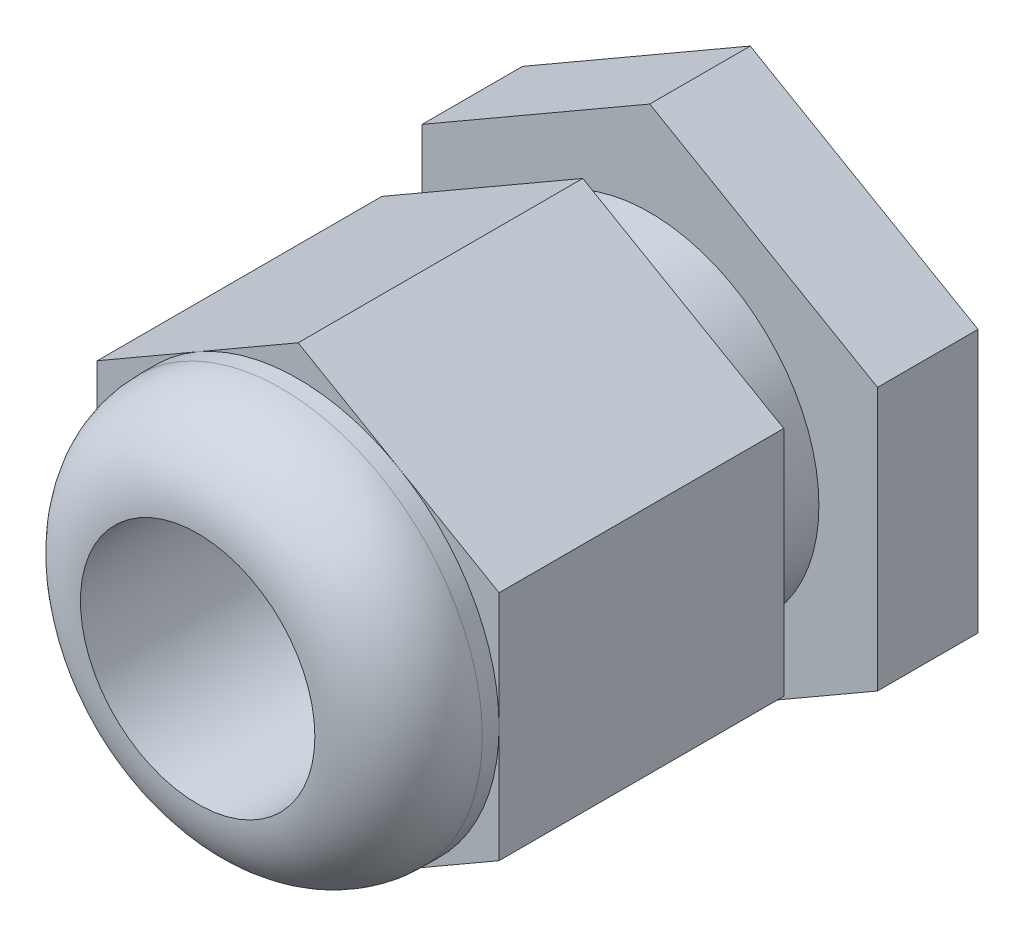
SolidWorks part; units mm, degrees
ref_plane "Plano frontal" through (0, 0, 0) normal (0, 0, 1) x (1, 0, 0)
ref_plane "Plano superior" through (0, 0, 0) normal (0, 1, 0) x (1, 0, 0)
ref_plane "Plano direito" through (0, 0, 0) normal (1, 0, 0) x (0, 0, -1)
sketch "Esboço1" plane through (0, 0, 0) normal (0, 0, 1) x (1, 0, 0)
  line L1 (0, 13.8564) -> (-12, 6.9282)
  line L2 (-12, 6.9282) -> (-12, -6.9282)
  line L3 (-12, -6.9282) -> (0, -13.8564)
  line L4 (0, -13.8564) -> (12, -6.9282)
  line L5 (12, -6.9282) -> (12, 6.9282)
  line L6 (12, 6.9282) -> (0, 13.8564)
  circle A0 centre (0, 0) radius 12 construction
extrude "Ressalto-extrusão1" add sketch "Esboço1" along normal mid plane 17
sketch "Esboço2" plane through (0, 0, 8.5) normal (0, 0, 1) x (1, 0, 0)
  circle A0 centre (0, 0) radius 12
extrude "Ressalto-extrusão2" add sketch "Esboço2" along normal blind 6
fillet "Filete1" radius 5 1 edges at (12, 0, 14.5)
sketch "Esboço3" plane through (0, 0, -8.5) normal (0, 0, -1) x (-1, 0, 0)
  circle A0 centre (0, 0) radius 10.1
extrude "Ressalto-extrusão3" add sketch "Esboço3" along normal blind 10
sketch "Esboço4" plane through (0, 0, -18.5) normal (0, 0, -1) x (-1, 0, 0)
  line L1 (0, 15.7039) -> (-13.6, 7.852)
  line L2 (-13.6, 7.852) -> (-13.6, -7.852)
  line L3 (-13.6, -7.852) -> (0, -15.7039)
  line L4 (0, -15.7039) -> (13.6, -7.852)
  line L5 (13.6, -7.852) -> (13.6, 7.852)
  line L6 (13.6, 7.852) -> (0, 15.7039)
  circle A0 centre (0, 0) radius 13.6 construction
extrude "Ressalto-extrusão4" add sketch "Esboço4" against normal blind 6
sketch "Esboço5" plane through (0, 0, -18.5) normal (0, 0, -1) x (-1, 0, 0)
  circle A0 centre (0, 0) radius 10.1
extrude "Ressalto-extrusão5" add sketch "Esboço5" along normal blind 1
sketch "Esboço6" plane through (0, 0, 14.5) normal (0, 0, 1) x (1, 0, 0)
  circle A0 centre (0, 0) radius 7
extrude "Corte-extrusão1" cut sketch "Esboço6" against normal up to next
